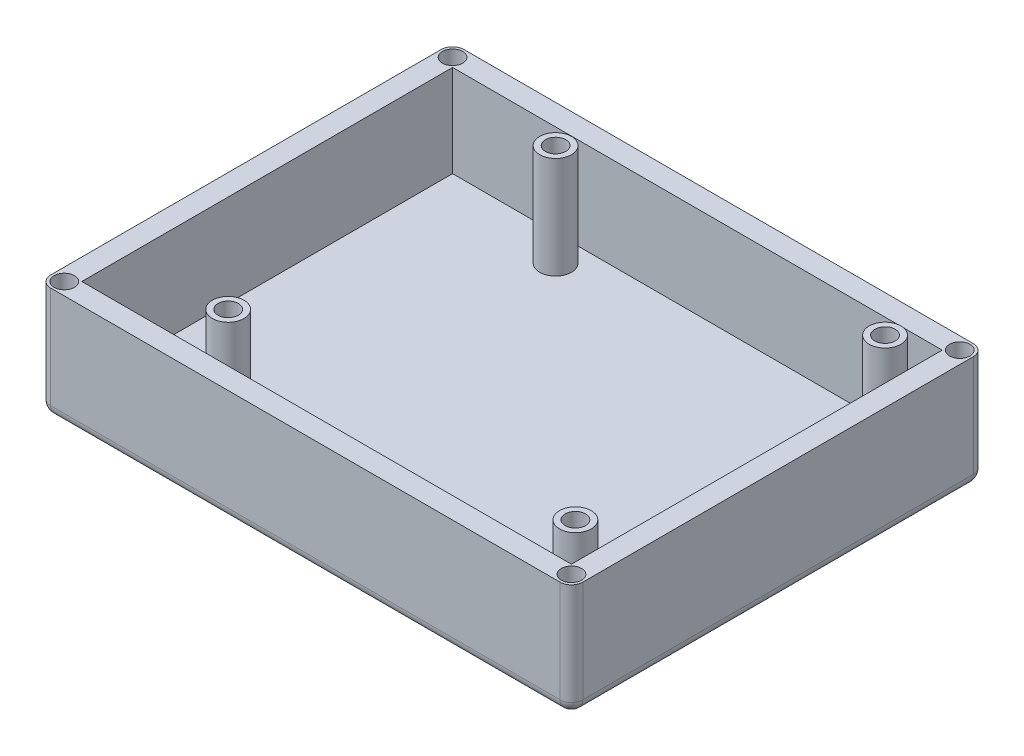
SolidWorks part; units mm, degrees
ref_plane "Front Plane" through (0, 0, 0) normal (0, 0, 1) x (1, 0, 0)
ref_plane "Top Plane" through (0, 0, 0) normal (0, 1, 0) x (1, 0, 0)
ref_plane "Right Plane" through (0, 0, 0) normal (1, 0, 0) x (0, 0, -1)
sketch "Sketch1" plane through (0, 0, 0) normal (0, 0, 1) x (1, 0, 0)
  line L1 (-59.69, 25.4) -> (59.69, 25.4)
  line L2 (-59.69, 25.4) -> (-59.69, 0)
  line L3 (-59.69, 0) -> (59.69, 0)
  line L4 (59.69, 25.4) -> (59.69, 0)
  point P4 (0, 0)
  dimension "D1" = 25.4
  dimension "D2" = 119.38
extrude "Boss-Extrude1" add sketch "Sketch1" along normal mid plane 92.71
sketch "Sketch2" plane through (0, 25.4, 0) normal (0, 1, 0) x (1, 0, 0)
  line L0 (59.69, 46.355) -> (-59.69, 46.355) construction
  line L1 (-54.9275, -41.5925) -> (54.9275, -41.5925)
  line L2 (-54.9275, -41.5925) -> (-54.9275, 41.5925)
  line L3 (-54.9275, 41.5925) -> (54.9275, 41.5925)
  line L4 (54.9275, -41.5925) -> (54.9275, 41.5925)
  line L5 (-54.9275, -41.5925) -> (54.9275, 41.5925) construction
  line L6 (-54.9275, 41.5925) -> (54.9275, -41.5925) construction
  line L7 (59.69, -46.355) -> (59.69, 46.355) construction
  point P0 (0, 0)
  dimension "D1" = 4.7625
  dimension "D2" = 4.7625
extrude "Cut-Extrude1" cut sketch "Sketch2" against normal offset from surface (20.6375 mm away) 4.7625 up to face at (0, 0, 0)
fillet "Fillet1" radius 2.54 4 edges at (59.69, 12.7, -46.355) (-59.69, 12.7, -46.355) (-59.69, 12.7, 46.355) (59.69, 12.7, 46.355)
sketch "Sketch6" plane through (0, 4.7625, 0) normal (0, 1, 0) x (1, 0, 0)
  line L0 (111.7366, 286.9927) -> (745.2477, 153.2391) construction
sketch "Sketch7" plane through (0, 4.7625, 0) normal (0, 1, 0) x (1, 0, 0)
  line L0 (255.5407, 500.0952) -> (944.874, 500.0952) construction
  line L1 (132.6927, 535.169) -> (847.3593, 535.169) construction
fillet "Fillet2" radius 2.54 8 edges at (-58.9461, 0, 45.6111) (0, 0, 46.355) (58.9461, 0, 45.6111) (59.69, 0, 0) (58.9461, 0, -45.6111) (0, 0, -46.355) (-58.9461, 0, -45.6111) (-59.69, 0, 0)
sketch "Sketch8" plane through (0, 25.4, 0) normal (0, 1, 0) x (1, 0, 0)
  line L0 (59.69, -43.815) -> (59.69, 43.815) construction
  line L1 (57.15, 46.355) -> (-57.15, 46.355) construction
  circle A3 centre (56.896, 43.561) radius 2.286
  dimension "D1" = 2.794
  dimension "D2" = 4.572
  dimension "D3" = 2.794
extrude "Cut-Extrude2" cut sketch "Sketch8" against normal blind 20.32
sketch "Sketch16" plane through (0, 25.4, 0) normal (0, 1, 0) x (1, 0, 0)
  line L0 (-59.69, -43.815) -> (-59.69, 43.815) construction
  line L1 (57.15, -46.355) -> (-57.15, -46.355) construction
  circle A0 centre (-56.896, -43.561) radius 2.286
  dimension "D1" = 4.572
  dimension "D3" = 2.794
  dimension "D2" = 2.794
extrude "Cut-Extrude4" cut sketch "Sketch16" against normal blind 20.32
sketch "Sketch17" plane through (0, 25.4, 0) normal (0, 1, 0) x (1, 0, 0)
  line L0 (59.69, -43.815) -> (59.69, 43.815) construction
  line L1 (57.15, -46.355) -> (-57.15, -46.355) construction
  circle A0 centre (56.896, -43.561) radius 2.286
  dimension "D1" = 4.572
  dimension "D2" = 2.794
  dimension "D3" = 2.794
extrude "Cut-Extrude5" cut sketch "Sketch17" against normal blind 20.32
sketch "Sketch18" plane through (0, 25.4, 0) normal (0, 1, 0) x (1, 0, 0)
  line L0 (57.15, 46.355) -> (-57.15, 46.355) construction
  line L1 (-59.69, -43.815) -> (-59.69, 43.815) construction
  circle A0 centre (-56.896, 43.561) radius 2.286
  dimension "D1" = 4.572
  dimension "D2" = 2.794
  dimension "D3" = 2.794
extrude "Cut-Extrude6" cut sketch "Sketch18" against normal blind 20.32
sketch "Sketch9" plane through (0, 4.7625, 0) normal (0, 1, 0) x (1, 0, 0)
  line L1 (54.9275, 41.5925) -> (54.9275, -41.5925) construction
  line L2 (-54.9275, 41.5925) -> (54.9275, 41.5925) construction
  circle A0 centre (-25.9715, 35.7505) radius 2.286
  circle A1 centre (-25.9715, 35.7505) radius 3.556
  dimension "D1" = 1.27
  dimension "D2" = 4.572
  dimension "D3" = 80.899
  dimension "D4" = 5.842
extrude "Boss-Extrude2" add sketch "Sketch9" along normal blind 22.86
sketch "Sketch11" plane through (0, 4.7625, 0) normal (0, 1, 0) x (1, 0, 0)
  line L0 (54.9275, 41.5925) -> (54.9275, -41.5925) construction
  line L2 (-54.9275, -41.5925) -> (54.9275, -41.5925) construction
  circle A0 centre (-30.8737, -32.8041) radius 3.556
  circle A1 centre (-30.8737, -32.8041) radius 2.286
  dimension "D1" = 4.572
  dimension "D2" = 1.27
  dimension "D3" = 85.8012
  dimension "D4" = 8.7884
extrude "Boss-Extrude3" add sketch "Sketch11" along normal blind 22.86
sketch "Sketch12" plane through (0, 4.7625, 0) normal (0, 1, 0) x (1, 0, 0)
  line L1 (54.9275, -41.5925) -> (54.9275, 41.5925) construction
  line L3 (-54.9275, 41.5925) -> (54.9275, 41.5925) construction
  circle A0 centre (47.8155, 35.8775) radius 3.556
  circle A1 centre (47.8155, 35.8775) radius 2.286
  dimension "D1" = 4.572
  dimension "D2" = 1.27
  dimension "D3" = 5.715
  dimension "D4" = 7.112
extrude "Boss-Extrude4" add sketch "Sketch12" along normal blind 22.86
sketch "Sketch13" plane through (0, 4.7625, 0) normal (0, 1, 0) x (1, 0, 0)
  line L0 (54.9275, 41.5925) -> (54.9275, -41.5925) construction
  line L1 (-54.9275, -41.5925) -> (54.9275, -41.5925) construction
  circle A0 centre (48.9585, -34.7345) radius 3.556
  circle A1 centre (48.9585, -34.7345) radius 2.286
  dimension "D1" = 4.572
  dimension "D2" = 1.27
  dimension "D3" = 5.969
  dimension "D4" = 6.858
extrude "Boss-Extrude5" add sketch "Sketch13" along normal blind 22.86
